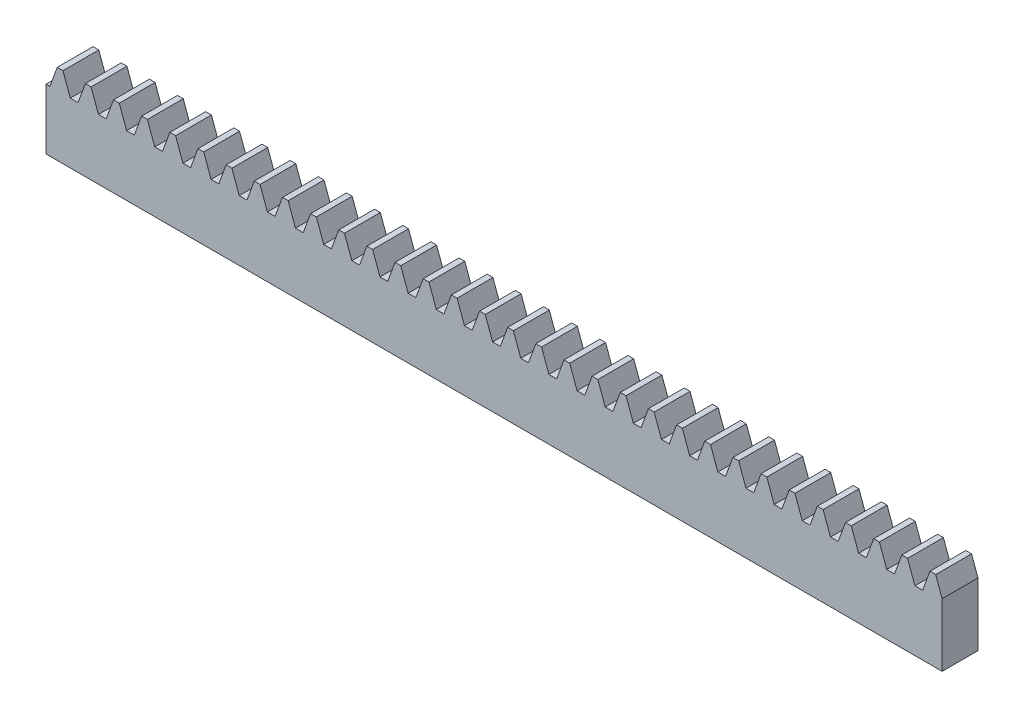
SolidWorks part; units mm, degrees
ref_plane "Plane1" through (0, 0, 0) normal (0, 0, 1) x (1, 0, 0)
ref_plane "Plane2" through (0, 0, 0) normal (0, 1, 0) x (1, 0, 0)
ref_plane "Plane3" through (0, 0, 0) normal (1, 0, 0) x (0, 0, -1)
sketch "HoldingSke" plane through (0, 0, 0) normal (0, 1, 0) x (1, 0, 0)
  line L0 (0, 0) -> (0.0278, 0.1981)
  line L1 (-15, 0) -> (100, 0) construction
  line L2 (0, 0) -> (-2.1039, 2.3779)
  line L3 (0, 0) -> (-11.863, 4.5341)
  line L4 (0, 0) -> (7.2428, 4.7035)
  line L5 (0, 0) -> (-23.7986, -8.8762)
  line L6 (0, 0) -> (-10.5278, -7.1032)
  line L9 (-71.009, 38.7566) -> (398.8373, 209.7667)
  line L10 (-76.2, 7.3779) -> (-36.2, 7.3779)
  line L11 (0, 0) -> (-20, 0)
  line L12 (-76.2, 101.6) -> (-76.033, 101.6)
  line L13 (24.9733, 27.94) -> (52.9518, 28.4284)
  line L14 (24.9733, 27.94) -> (24.9743, 27.94)
  line L15 (24.9733, 27.94) -> (100.4006, 29.5858)
  circle A0 centre (0, 0) radius 19.05
  circle A1 centre (0, 0) radius 20
  circle A2 centre (0, 0) radius 12.7
  dimension "MPH" = 40
  dimension "Diameter" = 38.1
  dimension "Num_teeth" = 33
  dimension "Pitch" = 0.2
  dimension "Width" = 20
  dimension "Show_teeth" = 998
  dimension "Thickness" = 12.7
  dimension "Ap" = 20
  dimension "Pitch_height" = 40
  dimension "Backlash" = 0.167
  dimension "Addendum_fac" = 1
  dimension "Dedendum_fac" = 1.25
  dimension "Clearance_fac" = 0.25
  dimension "Dedendum_add" = 0.001
  dimension "Length" = 500
  dimension "Module" = 5
sketch "BlankSke" plane through (0, 0, 0) normal (0, 0, 1) x (1, 0, 0)
  line L1 (0, 0) -> (500, 0)
  line L2 (0, 0) -> (0, 45)
  line L3 (0, 45) -> (500, 45)
  line L4 (500, 0) -> (500, 45)
  dimension "Length" = 500
  dimension "Blank_height" = 45
extrude "Blank" add sketch "BlankSke" against normal blind 20
sketch "TooCutSkeIll" plane through (0, 0, 0) normal (0, 0, 1) x (1, 0, 0)
  line L0 (-6.1999, 44.8684) -> (-2.4528, 34.5731)
  line L1 (-1.2772, 33.75) -> (1.2772, 33.75)
  line L2 (2.4528, 34.5731) -> (6.1999, 44.8684)
  line L3 (500, 45) -> (0, 45) construction
  line L4 (0, 0) -> (0, 64.897) construction
  line L5 (-13.208, 40) -> (12.954, 40) construction
  line L6 (0, 0) -> (500, 0) construction
  line L7 (4.428, 40) -> (4.428, 48.7463) construction
  line L8 (-4.428, 40) -> (-4.428, 48.7463) construction
  line L9 (6.3879, 45) -> (6.3879, 45.0254)
  line L10 (-6.3879, 45) -> (-6.3879, 45.0254)
  line L11 (-6.3879, 45.0254) -> (6.3879, 45.0254)
  arc A0 (1.2772, 33.75) -> (2.4528, 34.5731) centre (1.2772, 35.001) ccw
  arc A1 (-2.4528, 34.5731) -> (-1.2772, 33.75) centre (-1.2772, 35.001) ccw
  arc A2 (6.3879, 45) -> (6.1999, 44.8684) centre (6.3879, 44.8) ccw
  arc A3 (-6.1999, 44.8684) -> (-6.3879, 45) centre (-6.3879, 44.8) ccw
  dimension "Root_fillet" = 1.251
  dimension "Break_rad" = 0.2
  dimension "Pitch_height" = 40
  dimension "Gap_width" = 8.856
  dimension "Dedendum" = 6.25
  dimension "Addendum_plus" = 5.0254
  dimension "Pressure_angle" = 20
extrude "ToothCutIll" [suppressed] cut sketch "TooCutSkeIll" against normal through all
sketch "TooCutSkeSim" plane through (0, 0, 0) normal (0, 0, 1) x (1, 0, 0)
  line L0 (2.1532, 33.75) -> (-2.1532, 33.75)
  line L1 (6.2571, 45.0254) -> (2.1532, 33.75)
  line L2 (0, 17.4625) -> (0, 53.467) construction
  line L3 (6.2571, 45.0254) -> (-6.2571, 45.0254)
  line L6 (-6.2571, 45.0254) -> (-2.1532, 33.75)
  line L9 (-4.428, 40) -> (4.428, 40) construction
  line L10 (0, 0) -> (500, 0) construction
  line L11 (4.428, 40) -> (4.428, 53.467) construction
  line L12 (-4.428, 40) -> (-4.428, 53.467) construction
  dimension "Pitch_height" = 40
  dimension "Pressure_angle" = 20
  dimension "Gap_width" = 8.856
  dimension "Dedendum" = 6.25
  dimension "Addendum_plus" = 5.0254
extrude "ToothCutSim" cut sketch "TooCutSkeSim" against normal through all
pattern_linear "TeethCuts" count 32 spacing 15.708 along (1, 0, 0) of "ToothCutIll", "ToothCutSim"
equation "' \"Module@HoldingSke\" = 6.35"
equation "' \"Num_teeth@HoldingSke\" = 12"
equation "' \"Ap@HoldingSke\" =  20"
equation "' \"Width@HoldingSke\" = 0.25 * 25.4"
equation "' \"Show_teeth@HoldingSke\" = 500"
equation "' \"Backlash@HoldingSke\" = 0.009 * 25.4"
equation "' \"Addendum_fac@HoldingSke\" = 1.0"
equation "' \"Dedendum_fac@HoldingSke\" = 1.25"
equation "' \"Dedendum_add@HoldingSke\" = 0.00005 * 25.4"
equation "' \"Clearance_fac@HoldingSke\" = 0.25"
equation "' \"Pitch_height@HoldingSke\" = 1 * 25.4"
equation "' \"Length@HoldingSke\" = 4.71 * 25.4"
equation "\"Pitch@HoldingSke\" = 1 / \"Module@HoldingSke\""
equation "\"MPH@HoldingSke\" = \"Dedendum_fac@HoldingSke\" / \"Pitch@HoldingSke\" + 2 * \"Dedendum_add@HoldingSke\" + 0.002 * 25.4"
equation "\"MPH@HoldingSke\" = ((sgn( \"MPH@HoldingSke\" - \"Pitch_height@HoldingSke\")+1)*( \"MPH@HoldingSke\" - \"Pitch_height@HoldingSke\"))/2 + \"Pitch_height@HoldingSke\""
equation "\"Blank_height@BlankSke\" = \"Pitch_height@HoldingSke\" + \"Addendum_fac@HoldingSke\"  / \"Pitch@HoldingSke\" "
equation "\"Length@BlankSke\" =  \"Length@HoldingSke\""
equation "\"Face_width@Blank\" = \"Width@HoldingSke\""
equation "\"Pressure_angle@TooCutSkeIll\" = \"Ap@HoldingSke\""
equation "\"Addendum_plus@TooCutSkeIll\" =  \"Addendum_fac@HoldingSke\"  / \"Pitch@HoldingSke\" + 0.001 *25.4"
equation "\"Dedendum@TooCutSkeIll\" = \"Dedendum_fac@HoldingSke\"  / \"Pitch@HoldingSke\""
equation "\"Pitch_height@TooCutSkeIll\" =  \"MPH@HoldingSke\""
equation "\"Gap_width@TooCutSkeIll\" = 3.14159265 / 2 / \"Pitch@HoldingSke\" + 6 * \"Backlash@HoldingSke\""
equation "\"Pressure_angle@TooCutSkeSim\" = \"Ap@HoldingSke\""
equation "\"Addendum_plus@TooCutSkeSim\" =  \"Addendum_fac@HoldingSke\"  / \"Pitch@HoldingSke\" + 0.001 * 25.4"
equation "\"Dedendum@TooCutSkeSim\" = \"Dedendum_fac@HoldingSke\"  / \"Pitch@HoldingSke\""
equation "\"Pitch_height@TooCutSkeSim\" =  \"MPH@HoldingSke\""
equation "\"Gap_width@TooCutSkeSim\" = 3.14159265 / 2 / \"Pitch@HoldingSke\" + 6 * \"Backlash@HoldingSke\""
equation "\"Root_fillet@TooCutSkeIll\" = \"Clearance_fac@HoldingSke\" / \"Pitch@HoldingSke\" + \"Dedendum_add@HoldingSke\""
equation "\"Break_rad@TooCutSkeIll\" = 0.02 / \"Pitch@HoldingSke\" * 2"
equation "\"Linear_pitch@TeethCuts\" = 3.14159265 / \"Pitch@HoldingSke\""
equation "\"Num_teeth@HoldingSke\" = int( ( \"Length@HoldingSke\" + 0 ) / (3.14159265 / \"Pitch@HoldingSke\")) + 0.9999  + 1"
equation " \"Num_teeth@TeethCuts\" = int( \"Show_teeth@HoldingSke\" ) + 1"
equation " \"Num_teeth@TeethCuts\" = ((sgn( \"Num_teeth@TeethCuts\" - \"Num_teeth@HoldingSke\" )-1)*( \"Num_teeth@TeethCuts\" - \"Num_teeth@HoldingSke\" ))/-2+ \"Num_teeth@HoldingSke\""
equation " \"Num_teeth@TeethCuts\" = ((sgn( \"Num_teeth@TeethCuts\" - 2.0)+1)*( \"Num_teeth@TeethCuts\" - 2.0))/2 +2.0"
